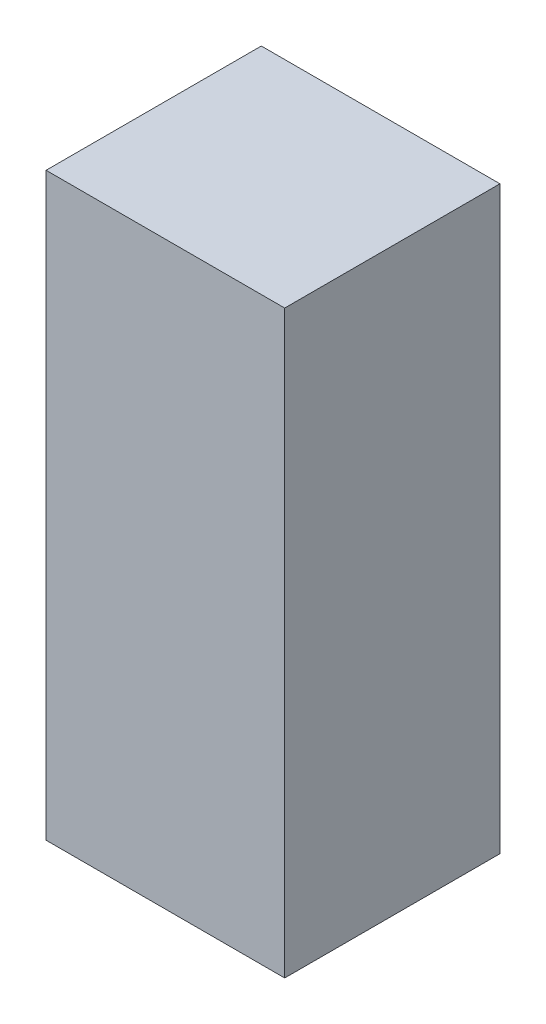
SolidWorks part; units mm, degrees
ref_plane "Front Plane" through (0, 0, 0) normal (0, 0, 1) x (1, 0, 0)
ref_plane "Top Plane" through (0, 0, 0) normal (0, 1, 0) x (1, 0, 0)
ref_plane "Right Plane" through (0, 0, 0) normal (1, 0, 0) x (0, 0, -1)
sketch "Sketch1" plane through (0, 0, 0) normal (0, 1, 0) x (1, 0, 0)
  line L1 (323.85, -292.1) -> (-323.85, -292.1)
  line L2 (323.85, -292.1) -> (323.85, 292.1)
  line L3 (323.85, 292.1) -> (-323.85, 292.1)
  line L4 (-323.85, -292.1) -> (-323.85, 292.1)
  line L5 (323.85, -292.1) -> (-323.85, 292.1) construction
  line L6 (323.85, 292.1) -> (-323.85, -292.1) construction
  point P0 (0, 0)
  dimension "D1" = 647.7
  dimension "D2" = 584.2
extrude "Boss-Extrude1" add sketch "Sketch1" along normal blind 1574.8
